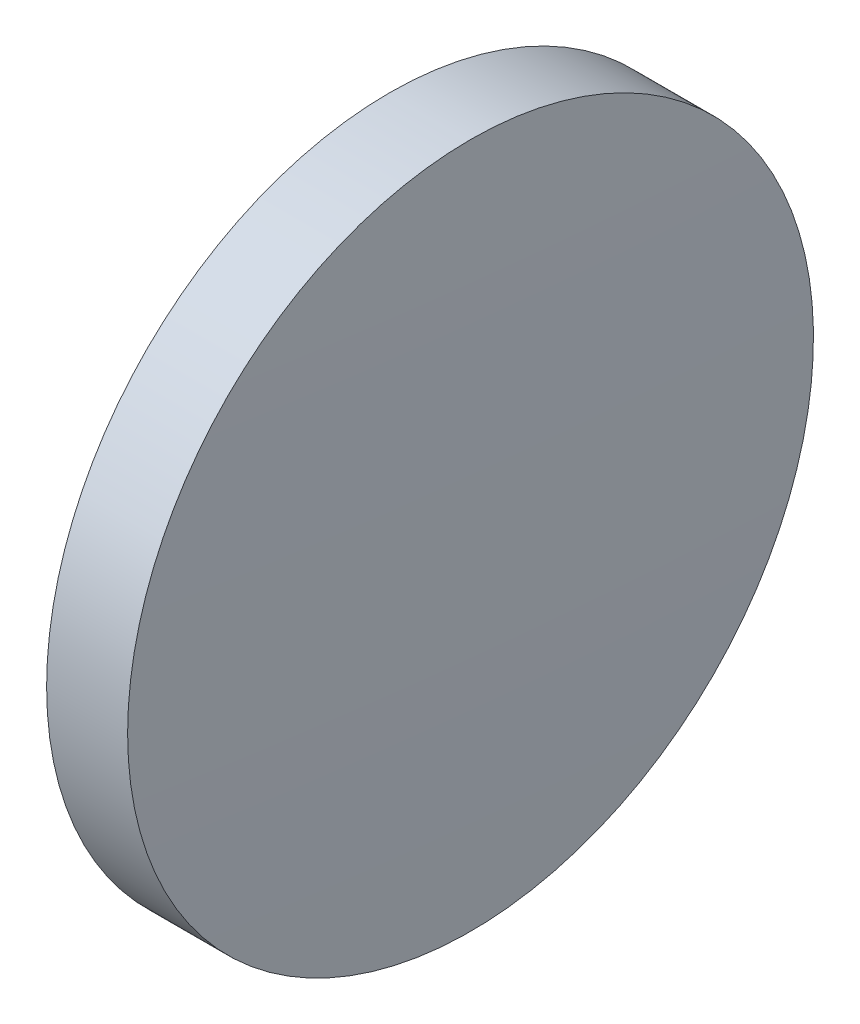
SolidWorks part; units mm, degrees
ref_plane "前视基准面" through (0, 0, 0) normal (0, 0, 1) x (1, 0, 0)
ref_plane "上视基准面" through (0, 0, 0) normal (0, 1, 0) x (1, 0, 0)
ref_plane "右视基准面" through (0, 0, 0) normal (1, 0, 0) x (0, 0, -1)
sketch "草图1" plane through (0, 0, 0) normal (0, 0, 1) x (1, 0, 0)
  line L0 (83.372, 48.6161) -> (89.8656, 48.6161) construction
  line L1 (84.9582, 61.3161) -> (87.9582, 61.3161)
  line L2 (87.9582, 61.3161) -> (87.9582, 35.9161)
  line L3 (87.9582, 35.9161) -> (84.9582, 35.9161)
  line L4 (84.9582, 35.9161) -> (84.9582, 61.3161)
  arc A0 (84.9582, 61.3161) -> (84.9582, 35.9161) centre (545.8556, 48.6161) ccw
  arc A1 (87.9582, 35.9161) -> (87.9582, 61.3161) centre (-372.9392, 48.6161) ccw
  dimension "D1" = 25.4
  dimension "D2" = 3
revolve "旋转1" add sketch "草图1" angle 360 about L0
